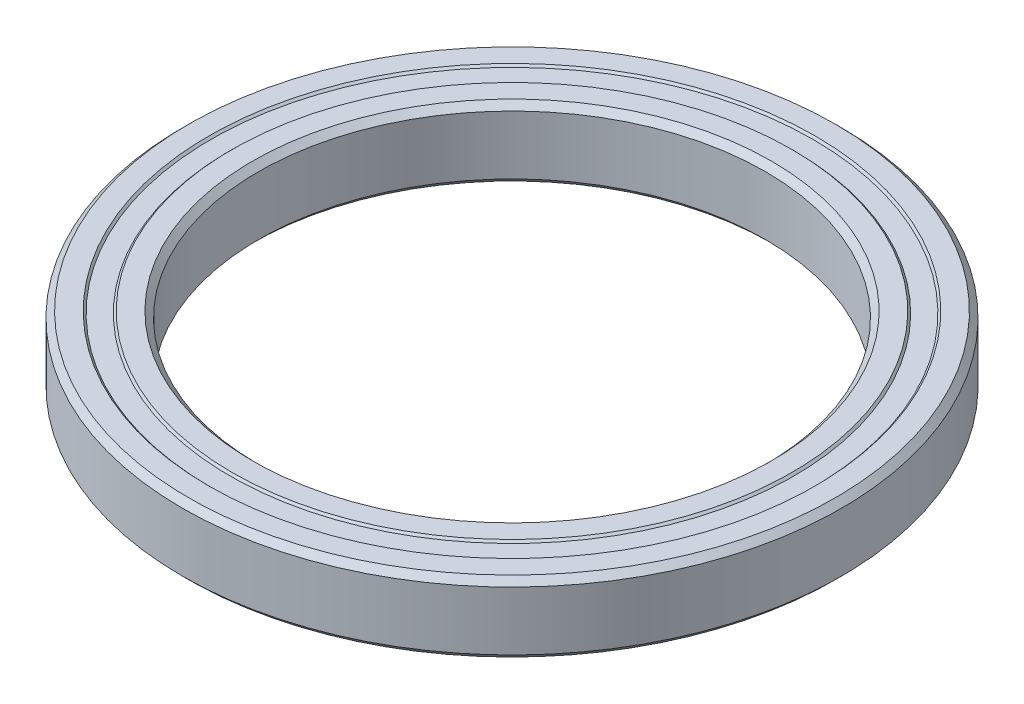
SolidWorks part; units mm, degrees
material "Stainless Steel (ferritic)"
ref_plane "Front Plane" through (0, 0, 0) normal (0, 0, 1) x (1, 0, 0)
ref_plane "Top Plane" through (0, 0, 0) normal (0, 1, 0) x (1, 0, 0)
ref_plane "Right Plane" through (0, 0, 0) normal (1, 0, 0) x (0, 0, -1)
sketch "Sketch1" plane through (0, 0, 0) normal (0, 0, 1) x (1, 0, 0)
  line L0 (0, -1.3494) -> (0, 70.5256) construction
  line L1 (25, 2.9) -> (25, -2.9)
  line L2 (25, -2.9) -> (25.6, -3.5)
  line L3 (25.6, -3.5) -> (27.6, -3.5)
  line L4 (27.6, -3.5) -> (27.8, -3.3)
  line L5 (27.8, -3.3) -> (29.7, -3.3)
  line L6 (29.7, -3.3) -> (29.9, -3.5)
  line L7 (29.9, -3.5) -> (31.9, -3.5)
  line L8 (31.9, -3.5) -> (32.5, -2.9)
  line L9 (32.5, -2.9) -> (32.5, 2.9)
  line L10 (32.5, 2.9) -> (31.9, 3.5)
  line L11 (31.9, 3.5) -> (29.9, 3.5)
  line L12 (29.9, 3.5) -> (29.7, 3.3)
  line L13 (29.7, 3.3) -> (27.8, 3.3)
  line L14 (27.8, 3.3) -> (27.6, 3.5)
  line L15 (27.6, 3.5) -> (25.6, 3.5)
  line L16 (25.6, 3.5) -> (25, 2.9)
  line L17 (0, 0) -> (25, 0) construction
  dimension "D1" = 25
  dimension "D2" = 7
  dimension "D3" = 0.6
  dimension "D4" = 0.2
  dimension "D5" = 32.5
  dimension "D6" = 2
revolve "Revolve1" add sketch "Sketch1" angle 360 about L0
